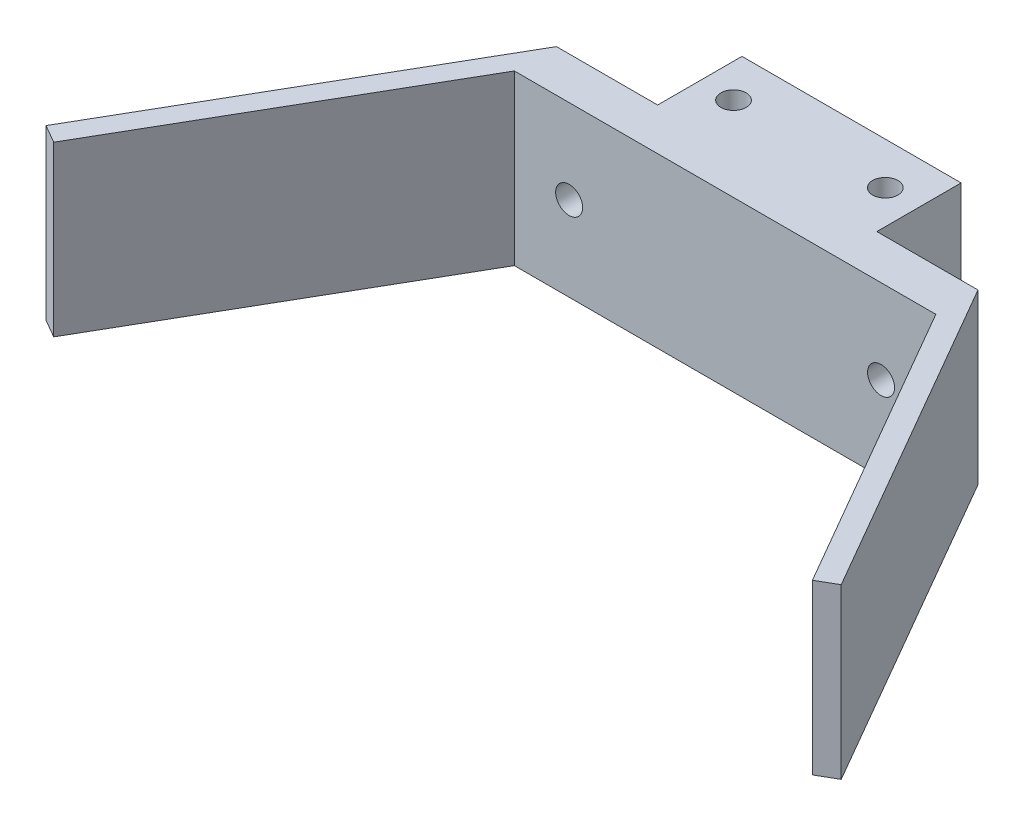
SolidWorks part; units mm, degrees
ref_plane "Plan de face" through (0, 0, 0) normal (0, 0, 1) x (1, 0, 0)
ref_plane "Plan de dessus" through (0, 0, 0) normal (0, 1, 0) x (1, 0, 0)
ref_plane "Plan de droite" through (0, 0, 0) normal (1, 0, 0) x (0, 0, -1)
sketch "Esquisse1" plane through (0, 0, 0) normal (0, 0, 1) x (1, 0, 0)
  line L0 (-25, 0) -> (25, 0) construction
  line L1 (-25, -10) -> (25, -10)
  line L2 (-25, -10) -> (-25, 10)
  line L3 (-25, 10) -> (25, 10)
  line L4 (25, -10) -> (25, 10)
  line L5 (-25, -10) -> (25, 10) construction
  line L6 (-25, 10) -> (25, -10) construction
  line L8 (0, 10) -> (0, -10) construction
  circle A0 centre (-18.5, 0) radius 1.6
  circle A1 centre (18.5, 0) radius 1.6
  point P0 (0, 0)
  dimension "D3" = 18.5
  dimension "D4" = 3.2
  dimension "D1" = 50
  dimension "D2" = 20
extrude "Boss.-Extru.1" add sketch "Esquisse1" along normal blind 5
sketch "Esquisse2" plane through (0, 10, 0) normal (0, 1, 0) x (1, 0, 0)
  line L0 (25, 0) -> (25, -5)
  line L1 (25, -5) -> (45, -39.641)
  line L2 (45, -39.641) -> (47.1651, -38.391)
  line L3 (47.1651, -38.391) -> (25, 0)
  line L4 (0, -30.8194) -> (0, 0) construction
  line L5 (25, -5) -> (25, -30.8194) construction
  line L6 (-45, -39.641) -> (-47.1651, -38.391)
  line L7 (-25, -5) -> (-45, -39.641)
  line L8 (-47.1651, -38.391) -> (-25, 0)
  line L9 (-25, 0) -> (-25, -5)
  line L10 (-13, 10) -> (13, 10)
  line L11 (13, 10) -> (13, 0)
  line L12 (25, 0) -> (-25, 0) construction
  line L13 (13, 0) -> (-13, 0)
  line L14 (-13, 10) -> (-13, 0)
  line L15 (0, 0) -> (0, 10) construction
  line L17 (13, 5) -> (-13, 5) construction
  circle A0 centre (-9, 5) radius 1.5
  circle A1 centre (9, 5) radius 1.5
  point P21 (0, 10)
  dimension "D5" = 3
  dimension "D1" = 30
  dimension "D2" = 40
  dimension "D3" = 13
  dimension "D4" = 10
  dimension "D6" = 9
extrude "Boss.-Extru.2" add sketch "Esquisse2" against normal blind 20
